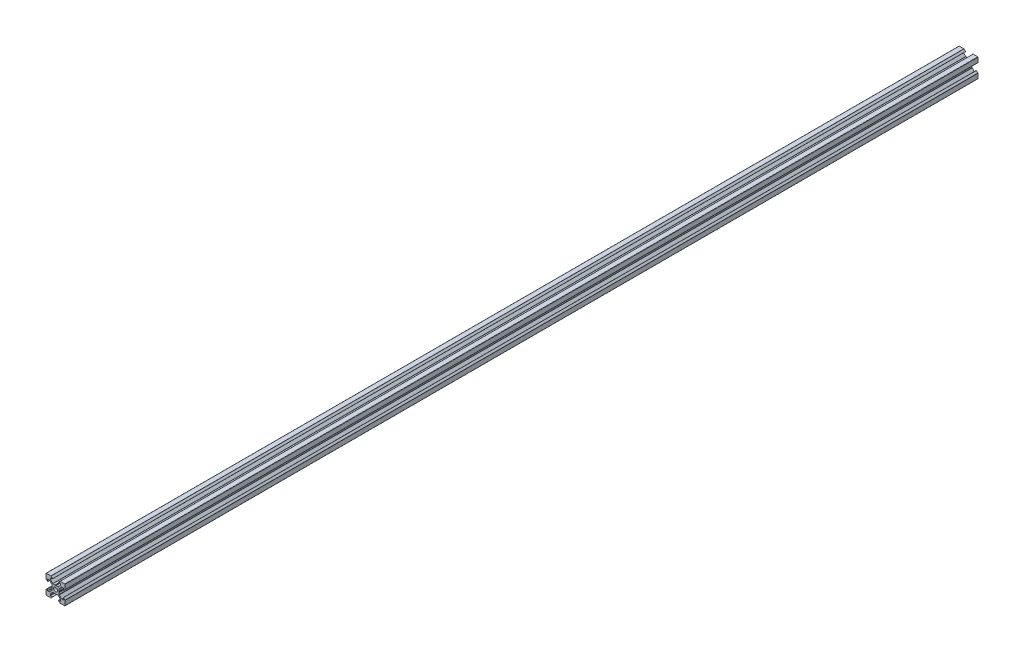
SolidWorks part; units mm, degrees
material "6063-T5"
ref_plane "Plan de face" through (0, 0, 0) normal (0, 0, 1) x (1, 0, 0)
ref_plane "Plan de dessus" through (0, 0, 0) normal (0, 1, 0) x (1, 0, 0)
ref_plane "Plan de droite" through (0, 0, 0) normal (1, 0, 0) x (0, 0, -1)
sketch "Esquisse1" plane through (0, 0, 0) normal (0, 0, 1) x (1, 0, 0)
  line L0 (18.7749, -2.8952) -> (18.7749, -4.8946)
  line L1 (18.4749, -5.1946) -> (17.2591, -5.1946)
  line L2 (17.047, -5.1067) -> (14.5634, -2.6231)
  line L3 (14.4755, -2.411) -> (14.4755, -0.2148)
  line L4 (14.4755, -0.2148) -> (14.1755, 0.3048)
  line L5 (14.1755, 0.3048) -> (14.4755, 0.8244)
  line L6 (14.4755, 0.8244) -> (14.4755, 3.0205)
  line L7 (14.5634, 3.2326) -> (17.047, 5.7162)
  line L8 (17.2591, 5.8041) -> (18.4749, 5.8041)
  line L9 (18.7749, 5.5041) -> (18.7749, 3.5048)
  line L10 (18.9456, 3.4341) -> (20.487, 4.9755)
  line L11 (20.5749, 5.1876) -> (20.5749, 10.0048)
  line L12 (20.2749, 10.3048) -> (15.4577, 10.3048)
  line L13 (15.2456, 10.2169) -> (13.7041, 8.6755)
  line L14 (13.7749, 8.5048) -> (15.7742, 8.5048)
  line L15 (16.0742, 8.2048) -> (16.0742, 6.989)
  line L16 (15.9863, 6.7769) -> (13.5027, 4.2933)
  line L17 (13.2906, 4.2054) -> (11.0945, 4.2054)
  line L18 (11.0945, 4.2054) -> (10.5749, 3.9054)
  line L19 (10.5749, 3.9054) -> (10.0552, 4.2054)
  line L20 (10.0552, 4.2054) -> (7.8591, 4.2054)
  line L21 (7.647, 4.2933) -> (5.1634, 6.7769)
  line L22 (5.0755, 6.989) -> (5.0755, 8.2048)
  line L23 (5.3755, 8.5048) -> (7.3749, 8.5048)
  line L24 (7.4456, 8.6755) -> (5.9041, 10.2169)
  line L25 (5.692, 10.3048) -> (0.8749, 10.3048)
  line L26 (0.5749, 10.0048) -> (0.5749, 5.1876)
  line L27 (0.6627, 4.9755) -> (2.2041, 3.4341)
  line L28 (2.3749, 3.5048) -> (2.3749, 5.5041)
  line L29 (2.6749, 5.8041) -> (3.8906, 5.8041)
  line L30 (4.1027, 5.7162) -> (6.5863, 3.2326)
  line L31 (6.6742, 3.0205) -> (6.6742, 0.8244)
  line L32 (6.6742, 0.8244) -> (6.9742, 0.3048)
  line L33 (6.9742, 0.3048) -> (6.6742, -0.2148)
  line L34 (6.6742, -0.2148) -> (6.6742, -2.411)
  line L35 (6.5863, -2.6231) -> (4.1027, -5.1067)
  line L36 (3.8906, -5.1946) -> (2.6749, -5.1946)
  line L37 (2.3749, -4.8946) -> (2.3749, -2.8952)
  line L38 (2.2041, -2.8245) -> (0.6627, -4.3659)
  line L39 (0.5749, -4.5781) -> (0.5749, -9.3952)
  line L40 (0.8749, -9.6952) -> (5.692, -9.6952)
  line L41 (5.9041, -9.6074) -> (7.4456, -8.0659)
  line L42 (7.3749, -7.8952) -> (5.3755, -7.8952)
  line L43 (5.0755, -7.5952) -> (5.0755, -6.3795)
  line L44 (5.1634, -6.1674) -> (7.647, -3.6838)
  line L45 (7.8591, -3.5959) -> (10.0552, -3.5959)
  line L46 (10.0552, -3.5959) -> (10.5749, -3.2959)
  line L47 (10.5749, -3.2959) -> (11.0945, -3.5959)
  line L48 (11.0945, -3.5959) -> (13.2906, -3.5959)
  line L49 (13.5027, -3.6838) -> (15.9863, -6.1674)
  line L50 (16.0742, -6.3795) -> (16.0742, -7.5952)
  line L51 (15.7742, -7.8952) -> (13.7749, -7.8952)
  line L52 (13.7041, -8.0659) -> (15.2456, -9.6074)
  line L53 (15.4577, -9.6952) -> (20.2749, -9.6952)
  line L54 (20.5749, -9.3952) -> (20.5749, -4.5781)
  line L55 (20.487, -4.3659) -> (18.9456, -2.8245)
  arc A0 (10.5749, -1.7952) -> (12.6749, 0.3048) centre (10.5749, 0.3048) ccw
  arc A1 (12.6749, 0.3048) -> (10.5749, 2.4048) centre (10.5749, 0.3048) ccw
  arc A2 (10.5749, 2.4048) -> (8.4749, 0.3048) centre (10.5749, 0.3048) ccw
  arc A3 (8.4749, 0.3048) -> (10.5749, -1.7952) centre (10.5749, 0.3048) ccw
  arc A4 (18.9456, -2.8245) -> (18.7749, -2.8952) centre (18.8749, -2.8952) ccw
  arc A5 (18.4749, -5.1946) -> (18.7749, -4.8946) centre (18.4749, -4.8946) ccw
  arc A6 (17.047, -5.1067) -> (17.2591, -5.1946) centre (17.2591, -4.8946) ccw
  arc A7 (14.4755, -2.411) -> (14.5634, -2.6231) centre (14.7755, -2.411) ccw
  arc A8 (14.5634, 3.2326) -> (14.4755, 3.0205) centre (14.7755, 3.0205) ccw
  arc A9 (17.2591, 5.8041) -> (17.047, 5.7162) centre (17.2591, 5.5041) ccw
  arc A10 (18.7749, 5.5041) -> (18.4749, 5.8041) centre (18.4749, 5.5041) ccw
  arc A11 (18.7749, 3.5048) -> (18.9456, 3.4341) centre (18.8749, 3.5048) ccw
  arc A12 (20.487, 4.9755) -> (20.5749, 5.1876) centre (20.2749, 5.1876) ccw
  arc A13 (20.5749, 10.0048) -> (20.2749, 10.3048) centre (20.2749, 10.0048) ccw
  arc A14 (15.4577, 10.3048) -> (15.2456, 10.2169) centre (15.4577, 10.0048) ccw
  arc A15 (13.7041, 8.6755) -> (13.7749, 8.5048) centre (13.7749, 8.6048) ccw
  arc A16 (16.0742, 8.2048) -> (15.7742, 8.5048) centre (15.7742, 8.2048) ccw
  arc A17 (15.9863, 6.7769) -> (16.0742, 6.989) centre (15.7742, 6.989) ccw
  arc A18 (13.2906, 4.2054) -> (13.5027, 4.2933) centre (13.2906, 4.5054) ccw
  arc A19 (7.647, 4.2933) -> (7.8591, 4.2054) centre (7.8591, 4.5054) ccw
  arc A20 (5.0755, 6.989) -> (5.1634, 6.7769) centre (5.3755, 6.989) ccw
  arc A21 (5.3755, 8.5048) -> (5.0755, 8.2048) centre (5.3755, 8.2048) ccw
  arc A22 (7.3749, 8.5048) -> (7.4456, 8.6755) centre (7.3749, 8.6048) ccw
  arc A23 (5.9041, 10.2169) -> (5.692, 10.3048) centre (5.692, 10.0048) ccw
  arc A24 (0.8749, 10.3048) -> (0.5749, 10.0048) centre (0.8749, 10.0048) ccw
  arc A25 (0.5749, 5.1876) -> (0.6627, 4.9755) centre (0.8749, 5.1876) ccw
  arc A26 (2.2041, 3.4341) -> (2.3749, 3.5048) centre (2.2749, 3.5048) ccw
  arc A27 (2.6749, 5.8041) -> (2.3749, 5.5041) centre (2.6749, 5.5041) ccw
  arc A28 (4.1027, 5.7162) -> (3.8906, 5.8041) centre (3.8906, 5.5041) ccw
  arc A29 (6.6742, 3.0205) -> (6.5863, 3.2326) centre (6.3742, 3.0205) ccw
  arc A30 (6.5863, -2.6231) -> (6.6742, -2.411) centre (6.3742, -2.411) ccw
  arc A31 (3.8906, -5.1946) -> (4.1027, -5.1067) centre (3.8906, -4.8946) ccw
  arc A32 (2.3749, -4.8946) -> (2.6749, -5.1946) centre (2.6749, -4.8946) ccw
  arc A33 (2.3749, -2.8952) -> (2.2041, -2.8245) centre (2.2749, -2.8952) ccw
  arc A34 (0.6627, -4.3659) -> (0.5749, -4.5781) centre (0.8749, -4.5781) ccw
  arc A35 (0.5749, -9.3952) -> (0.8749, -9.6952) centre (0.8749, -9.3952) ccw
  arc A36 (5.692, -9.6952) -> (5.9041, -9.6074) centre (5.692, -9.3952) ccw
  arc A37 (7.4456, -8.0659) -> (7.3749, -7.8952) centre (7.3749, -7.9952) ccw
  arc A38 (5.0755, -7.5952) -> (5.3755, -7.8952) centre (5.3755, -7.5952) ccw
  arc A39 (5.1634, -6.1674) -> (5.0755, -6.3795) centre (5.3755, -6.3795) ccw
  arc A40 (7.8591, -3.5959) -> (7.647, -3.6838) centre (7.8591, -3.8959) ccw
  arc A41 (13.5027, -3.6838) -> (13.2906, -3.5959) centre (13.2906, -3.8959) ccw
  arc A42 (16.0742, -6.3795) -> (15.9863, -6.1674) centre (15.7742, -6.3795) ccw
  arc A43 (15.7742, -7.8952) -> (16.0742, -7.5952) centre (15.7742, -7.5952) ccw
  arc A44 (13.7749, -7.8952) -> (13.7041, -8.0659) centre (13.7749, -7.9952) ccw
  arc A45 (15.2456, -9.6074) -> (15.4577, -9.6952) centre (15.4577, -9.3952) ccw
  arc A46 (20.2749, -9.6952) -> (20.5749, -9.3952) centre (20.2749, -9.3952) ccw
  arc A47 (20.5749, -4.5781) -> (20.487, -4.3659) centre (20.2749, -4.5781) ccw
extrude "Boss.-Extru.1" add sketch "Esquisse1" along normal blind 960
